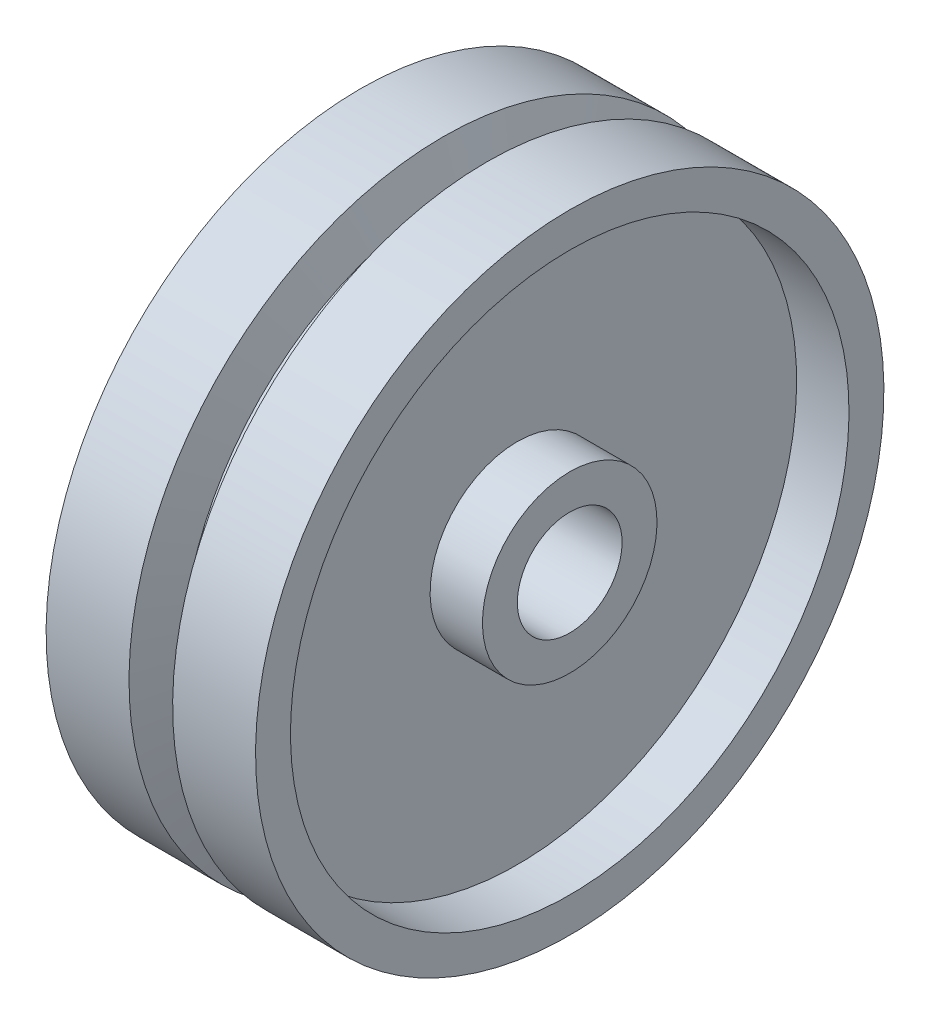
SolidWorks part; units mm, degrees
ref_plane "Alzado" through (0, 0, 0) normal (0, 0, 1) x (1, 0, 0)
ref_plane "Planta" through (0, 0, 0) normal (0, 1, 0) x (1, 0, 0)
ref_plane "Vista lateral" through (0, 0, 0) normal (1, 0, 0) x (0, 0, -1)
sketch "Croquis1" plane through (0, 0, 0) normal (0, 0, 1) x (1, 0, 0)
  line L0 (0, 0) -> (-12, 0) construction
  line L1 (0, 3) -> (-4.75, 3)
  line L2 (-12, 3) -> (-12, 5)
  line L3 (-12, 5) -> (-9, 5)
  line L4 (-9, 5) -> (-9, 16)
  line L5 (-9, 16) -> (-12, 16)
  line L6 (-12, 16) -> (-12, 18)
  line L7 (-12, 18) -> (-7.25, 18)
  line L8 (0, 18) -> (0, 16)
  line L9 (0, 16) -> (-3, 16)
  line L10 (-3, 16) -> (-3, 5)
  line L11 (-3, 5) -> (0, 5)
  line L12 (0, 5) -> (0, 3)
  line L13 (0, 0) -> (0, -18) construction
  line L18 (-6.5, 15.75) -> (-5.5, 15.75)
  line L19 (-7.25, 18) -> (-6.5, 15.75)
  line L20 (-5.5, 15.75) -> (-4.75, 18)
  line L21 (-4.75, 18) -> (0, 18)
  line L22 (-9, 10.5) -> (-3, 10.5) construction
  line L23 (-6.5, 5.25) -> (-5.5, 5.25)
  line L24 (-5.5, 5.25) -> (-4.75, 3)
  line L25 (-7.25, 3) -> (-6.5, 5.25)
  line L26 (-7.25, 3) -> (-12, 3)
  point P19 (-6, 17.25)
  point P24 (-6, 15.75)
  point P28 (-6, 5.25)
  dimension "D1" = 12
  dimension "D2" = 2
  dimension "D3" = 11
  dimension "D4" = 2.25
  dimension "D5" = 3
  dimension "D6" = 2
  dimension "D9" = 3
  dimension "D10" = 3
  dimension "D11" = 3
  dimension "D12" = 6
  dimension "D13" = 18
  dimension "D14" = 2.5
  dimension "D16" = 1
revolve "Revolución1" add sketch "Croquis1" angle 360 about L0
